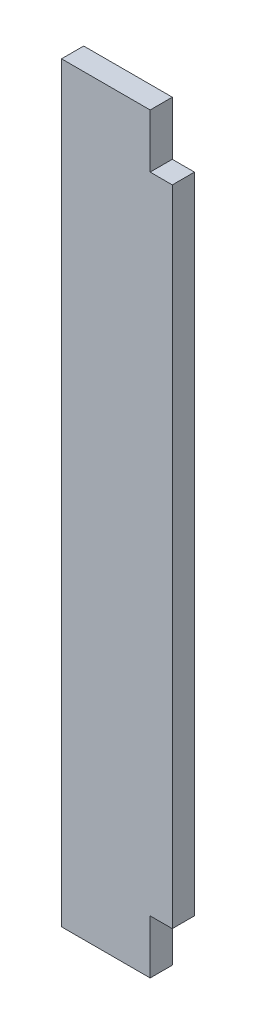
SolidWorks part; units mm, degrees
material "Pine"
ref_plane "Front Plane" through (0, 0, 0) normal (0, 0, 1) x (1, 0, 0)
ref_plane "Top Plane" through (0, 0, 0) normal (0, 1, 0) x (1, 0, 0)
ref_plane "Right Plane" through (0, 0, 0) normal (1, 0, 0) x (0, 0, -1)
sketch "Sketch1" plane through (0, 0, 0) normal (0, 0, 1) x (1, 0, 0)
  line L0 (8932.6508, -5243.5125) -> (10226.1458, -5243.5125)
  line L1 (9086.3208, -4722.0918) -> (10222.9708, -4853.7812)
  line L2 (8914.8708, -6342.0625) -> (10197.5708, -6342.0625)
  line L3 (8914.8708, -5808.6625) -> (10197.5708, -5808.6625)
  line L4 (8919.6333, -5253.0375) -> (10218.2083, -5253.0375)
  line L5 (9134.2633, -4656.1375) -> (9134.2633, -4638.3575)
  line L6 (9091.0833, -4638.3575) -> (9134.2633, -4638.3575)
  line L7 (9091.0833, -4567.2375) -> (9091.0833, -4638.3575)
  line L8 (9134.2633, -4656.1375) -> (9581.3033, -4656.1375)
  line L9 (9091.0833, -4567.2375) -> (9624.4833, -4567.2375)
  line L10 (9581.3033, -4656.1375) -> (9581.3033, -4638.3575)
  line L11 (9581.3033, -4638.3575) -> (9624.4833, -4638.3575)
  line L12 (9624.4833, -4567.2375) -> (9624.4833, -4638.3575)
  line L13 (8932.6508, -5225.7325) -> (9344.9775, -5225.7325)
  line L14 (8932.6508, -5256.2125) -> (8932.6508, -5243.5125)
  line L15 (8911.6958, -5256.2125) -> (8932.6508, -5256.2125)
  line L16 (8914.8708, -4722.0918) -> (9086.3208, -4722.0918)
  line L17 (8911.6958, -4715.5913) -> (8932.6508, -4715.5913)
  line L18 (8914.8708, -6342.0625) -> (8914.8708, -5808.6625)
  line L19 (12082.9917, -4722.0918) -> (10946.3417, -4853.7812)
  line L20 (12236.6617, -5243.5125) -> (10943.1667, -5243.5125)
  line L21 (10951.1042, -5253.0375) -> (12249.6792, -5253.0375)
  line L22 (10838.3917, -5656.2625) -> (11308.2917, -5656.2625)
  line L23 (10838.3917, -5719.7625) -> (11308.2917, -5719.7625)
  line L24 (10838.3917, -5742.5368) -> (11308.2917, -5742.5368)
  line L25 (10806.6417, -6342.0625) -> (11340.0417, -6342.0625)
  line L26 (10803.4667, -6335.7125) -> (11343.2167, -6335.7125)
  line L27 (10803.4667, -6317.9325) -> (11343.2167, -6317.9325)
  line L28 (10943.1667, -5225.7325) -> (11376.4483, -5225.7325)
  line L29 (11506.7292, -4754.5625) -> (10806.6417, -4827.5875)
  line L30 (11506.7292, -4567.2375) -> (11506.7292, -4754.5625)
  line L31 (10806.6417, -4567.2375) -> (10806.6417, -4827.5875)
  line L32 (10806.6417, -4567.2375) -> (11506.7292, -4567.2375)
  line L33 (10235.6708, -6329.3625) -> (10245.1958, -6329.3625)
  line L34 (10245.1958, -6329.3625) -> (10254.7208, -6278.5625)
  line L35 (10302.3458, -6329.3625) -> (10311.8708, -6278.5625)
  line L36 (10302.3458, -6329.3625) -> (10292.8208, -6329.3625)
  line L37 (10245.1958, -5821.3625) -> (10254.7208, -5872.1625)
  line L38 (10235.6708, -5821.3625) -> (10245.1958, -5821.3625)
  line L39 (10292.8208, -5821.3625) -> (10302.3458, -5821.3625)
  line L40 (10302.3458, -5821.3625) -> (10311.8708, -5872.1625)
  line L41 (10235.6708, -5821.3625) -> (10235.6708, -6329.3625)
  line L42 (10254.7208, -5872.1625) -> (10254.7208, -6278.5625)
  line L43 (10311.8708, -5872.1625) -> (10311.8708, -6278.5625)
  line L44 (10292.8208, -5821.3625) -> (10292.8208, -6329.3625)
  line L45 (8932.6508, -5225.7325) -> (8932.6508, -4715.5913)
  line L46 (8911.6958, -4715.5913) -> (8911.6958, -5256.2125)
  line L47 (8914.8708, -5248.275) -> (8914.8708, -4722.0918)
  line L48 (8919.6333, -5253.0375) -> (8914.8708, -5248.275)
  line L49 (8914.8708, -5145.0875) -> (8937.426, -5145.0875)
  line L50 (8914.8708, -5202.2375) -> (8937.426, -5202.2375)
  line L51 (10838.3917, -5656.2625) -> (10838.3917, -5719.7625)
  line L52 (10832.0417, -5736.1868) -> (10856.1717, -5736.1868)
  line L53 (10806.6417, -6342.0625) -> (10806.6417, -5818.7368)
  line L54 (10832.0417, -5649.9125) -> (10856.1717, -5649.9125)
  line L55 (10832.0417, -5726.1125) -> (10856.1717, -5726.1125)
  line L56 (10806.6417, -5818.7368) -> (10833.9015, -5818.7368)
  line L57 (10832.0417, -5806.0442) -> (10851.6815, -5806.0442)
  line L58 (10856.1717, -5801.5541) -> (10856.1717, -5736.1868)
  line L59 (10838.3917, -5814.2467) -> (10838.3917, -5742.5368)
  line L60 (10832.0417, -5806.0442) -> (10832.0417, -5736.1868)
  line L61 (10803.4667, -6317.9325) -> (10803.4667, -6335.7125)
  line L62 (10197.5708, -5808.6625) -> (10197.5708, -6342.0625)
  line L63 (9762.3842, -6348.4125) -> (9762.3842, -5802.3125)
  line L64 (9780.1642, -6348.4125) -> (9762.3842, -6348.4125)
  line L65 (9780.1642, -5802.3125) -> (9780.1642, -6348.4125)
  line L66 (9762.3842, -5802.3125) -> (9780.1642, -5802.3125)
  line L67 (9332.2775, -6348.4125) -> (9332.2775, -5802.3125)
  line L68 (9332.2775, -6348.4125) -> (9350.0575, -6348.4125)
  line L69 (9350.0575, -5802.3125) -> (9350.0575, -6348.4125)
  line L70 (9332.2775, -5802.3125) -> (9350.0575, -5802.3125)
  line L71 (9993.8374, -6061.075) -> (9993.8374, -6045.2418)
  line L72 (9998.5999, -6065.8375) -> (10014.4331, -6065.8375)
  line L73 (9998.5999, -6084.8875) -> (10014.4331, -6084.8875)
  line L74 (9993.8374, -6105.4832) -> (9993.8374, -6089.65)
  line L75 (9974.7874, -6105.4832) -> (9974.7874, -6089.65)
  line L76 (9954.1917, -6084.8875) -> (9970.0249, -6084.8875)
  line L77 (9974.7874, -6061.075) -> (9974.7874, -6045.2418)
  line L78 (9954.1917, -6065.8375) -> (9970.0249, -6065.8375)
  line L79 (10793.9417, -6237.2875) -> (10816.4969, -6237.2875)
  line L80 (10793.9417, -6294.4375) -> (10816.4969, -6294.4375)
  line L81 (10856.1717, -5649.9125) -> (10856.1717, -5726.1125)
  line L82 (10832.0417, -5726.1125) -> (10832.0417, -5649.9125)
  line L83 (10226.1458, -5225.7325) -> (10226.1458, -5243.5125)
  line L84 (10205.1908, -5257.8) -> (10205.1908, -4844.2499)
  line L85 (10230.9083, -4844.2499) -> (10230.9083, -5257.8)
  line L86 (10205.1908, -5257.8) -> (10230.9083, -5257.8)
  line L87 (10205.1908, -4844.2499) -> (10230.9083, -4844.2499)
  line L88 (10946.3417, -5176.8375) -> (10968.8969, -5176.8375)
  line L89 (9349.4676, -5141.9125) -> (9358.2674, -5141.9125)
  line L90 (10946.3417, -5119.6875) -> (10968.8969, -5119.6875)
  line L91 (9929.011, -4660.9635) -> (10066.0807, -4660.9635)
  line L92 (9929.011, -4678.7435) -> (10066.0807, -4678.7435)
  line L93 (10943.1667, -5225.7325) -> (10943.1667, -5243.5125)
  line L94 (10946.3417, -5248.275) -> (10951.1042, -5253.0375)
  line L95 (10946.3417, -5257.8063) -> (10946.3417, -4849.0188)
  line L96 (10964.1217, -5257.8) -> (10964.1217, -4844.2499)
  line L97 (10938.4042, -4844.2499) -> (10938.4042, -5257.8)
  line L98 (10938.4042, -5257.8) -> (10964.1217, -5257.8)
  line L99 (10964.1217, -4844.2499) -> (10938.4042, -4844.2499)
  line L100 (10344.8908, -4560.8875) -> (10369.0208, -4560.8875)
  line L101 (10344.8908, -4560.8875) -> (10369.0208, -4560.8875)
  line L102 (10800.2917, -4560.8875) -> (10824.4217, -4560.8875)
  line L103 (10200.4156, -5119.6875) -> (10222.9708, -5119.6875)
  line L104 (10200.4156, -5176.8375) -> (10222.9708, -5176.8375)
  line L105 (9344.9775, -5146.4026) -> (9344.9775, -5225.7325)
  line L106 (10344.8908, -4560.8875) -> (10344.8908, -4833.9375)
  line L107 (9792.8642, -5225.7325) -> (9792.8642, -5146.4026)
  line L108 (9362.7575, -5225.7325) -> (9775.0842, -5225.7325)
  line L109 (9680.3633, -4761.8396) -> (9680.3633, -4559.9604)
  line L110 (9656.2333, -4559.9604) -> (9680.3633, -4559.9604)
  line L111 (9656.2333, -4761.8396) -> (9680.3633, -4761.8396)
  line L112 (9656.2333, -4761.8396) -> (9656.2333, -4559.9604)
  line L113 (9779.5743, -5141.9125) -> (9788.374, -5141.9125)
  line L114 (10070.5708, -4665.4536) -> (10070.5708, -4674.2534)
  line L115 (9924.5208, -4674.2534) -> (9924.5208, -4665.4536)
  line L116 (12127.4417, -6188.3925) -> (12205.5015, -6188.3925)
  line L117 (12209.9917, -6170.6125) -> (12209.9917, -6183.9024)
  line L118 (9792.8642, -5225.7325) -> (10226.1458, -5225.7325)
  line L119 (9662.5833, -4754.5625) -> (10362.6708, -4827.5875)
  line L120 (9662.5833, -4567.2375) -> (9662.5833, -4754.5625)
  line L121 (10362.6708, -4567.2375) -> (10362.6708, -4827.5875)
  line L122 (9662.5833, -4567.2375) -> (10362.6708, -4567.2375)
  line L123 (10824.4217, -4833.9375) -> (10800.2917, -4833.9375)
  line L124 (10800.2917, -4833.9375) -> (10800.2917, -4560.8875)
  line L125 (10824.4217, -4560.8875) -> (10824.4217, -4833.9375)
  line L126 (10344.8908, -4833.9375) -> (10369.0208, -4833.9375)
  line L127 (10369.0208, -4833.9375) -> (10369.0208, -4560.8875)
  line L128 (10222.9708, -5248.275) -> (10218.2083, -5253.0375)
  line L129 (10222.9708, -5257.8063) -> (10222.9708, -4849.0188)
  line L130 (11734.6544, -5701.375) -> (11739.2301, -5701.375)
  line L131 (9362.7575, -5225.7325) -> (9362.7575, -5146.4026)
  line L132 (9775.0842, -5146.4026) -> (9775.0842, -5225.7325)
  line L133 (11761.3864, -5701.375) -> (11756.8282, -5701.375)
  line L134 (11734.6544, -5693.755) -> (11739.2301, -5693.755)
  line L135 (11761.4039, -5693.755) -> (11756.8282, -5693.755)
  line L136 (11734.6544, -5701.375) -> (11739.2301, -5701.375)
  line L137 (11744.3462, -5721.3024) -> (11744.3462, -5706.4179)
  line L138 (11751.7122, -5721.3024) -> (11751.7122, -5706.4179)
  line L139 (11740.0917, -6170.6125) -> (11740.0917, -6183.9024)
  line L140 (11689.2917, -6188.3925) -> (11822.6417, -6188.3925)
  line L141 (11689.2917, -6348.4093) -> (11689.2917, -6164.2657)
  line L142 (11689.2917, -6164.2657) -> (11746.4417, -6164.2657)
  line L143 (11746.4417, -6164.2657) -> (11746.4417, -6188.3925)
  line L144 (11689.2917, -6164.2657) -> (11746.4417, -6164.2657)
  line L145 (11340.0417, -5818.7368) -> (11340.0417, -6342.0625)
  line L146 (11290.5117, -5726.1125) -> (11314.6417, -5726.1125)
  line L147 (11290.5117, -5649.9125) -> (11290.5117, -5726.1125)
  line L148 (11340.0417, -5818.7368) -> (11312.7818, -5818.7368)
  line L149 (11314.6417, -5806.0442) -> (11295.0018, -5806.0442)
  line L150 (11290.5117, -5801.5541) -> (11290.5117, -5736.1868)
  line L151 (11308.2917, -5814.2467) -> (11308.2917, -5742.5368)
  line L152 (11314.6417, -5806.0442) -> (11314.6417, -5736.1868)
  line L153 (11290.5117, -5736.1868) -> (11314.6417, -5736.1868)
  line L154 (11848.0417, -6267.1325) -> (11962.3417, -6267.1325)
  line L155 (11962.3417, -6267.1325) -> (11962.3417, -6203.6325)
  line L156 (11343.2167, -6317.9325) -> (11343.2167, -6335.7125)
  line L157 (11365.4417, -5656.2625) -> (11365.4417, -5719.7625)
  line L158 (11365.4417, -5656.2625) -> (11479.7417, -5656.2625)
  line L159 (11778.1917, -6071.3937) -> (11802.3217, -6071.3937)
  line L160 (11314.6417, -5726.1125) -> (11314.6417, -5649.9125)
  line L161 (11314.6417, -5649.9125) -> (11290.5117, -5649.9125)
  line L162 (11308.2917, -5719.7625) -> (11308.2917, -5656.2625)
  line L163 (11689.2917, -6348.4093) -> (11713.4217, -6348.4093)
  line L164 (12203.6417, -6164.2657) -> (12260.7917, -6164.2657)
  line L165 (11713.4217, -6348.4093) -> (11713.4217, -6164.2657)
  line L166 (11695.6417, -6342.0625) -> (11695.6417, -6170.6125)
  line L167 (11695.6417, -6048.5337) -> (11699.4517, -6052.3437)
  line L168 (11822.6417, -6292.5325) -> (11822.6417, -6188.3925)
  line L169 (11695.6417, -6342.0625) -> (11695.6417, -6170.6125)
  line L170 (11848.0417, -6203.6325) -> (11962.3417, -6203.6325)
  line L171 (11848.0417, -6203.6325) -> (11848.0417, -6267.1325)
  line L172 (11987.7417, -6267.1325) -> (11987.7417, -6203.6325)
  line L173 (11784.5417, -6077.7437) -> (11784.5417, -6141.2438)
  line L174 (11517.8417, -5656.2625) -> (11632.1417, -5656.2625)
  line L175 (11632.1417, -5656.2625) -> (11632.1417, -5719.7625)
  line L176 (11632.1417, -5719.7625) -> (11517.8417, -5719.7625)
  line L177 (11517.8417, -5719.7625) -> (11517.8417, -5656.2625)
  line L178 (11692.4667, -6028.2137) -> (11692.4667, -6045.9937)
  line L179 (11695.6417, -5979.3188) -> (11718.1969, -5979.3188)
  line L180 (11695.6417, -5922.1687) -> (11718.1969, -5922.1687)
  line L181 (11821.0415, -5722.9375) -> (11821.0415, -5943.6)
  line L182 (11687.7042, -5651.5) -> (11701.9917, -5651.5)
  line L183 (11687.7042, -5651.5) -> (11687.7042, -6055.5251)
  line L184 (11687.7042, -6055.5251) -> (11701.9917, -6055.5251)
  line L185 (11701.9917, -6055.5251) -> (11701.9917, -5651.5)
  line L186 (11695.6417, -6055.2013) -> (11695.6417, -5649.595)
  line L187 (11695.6417, -5656.2625) -> (11695.6417, -6048.5337)
  line L188 (11695.6417, -6170.6125) -> (11740.0917, -6170.6125)
  line L189 (12203.6417, -6164.2657) -> (12203.6417, -6188.3925)
  line L190 (12254.4417, -6342.0625) -> (12254.4417, -6170.6125)
  line L191 (12129.0419, -5943.6) -> (12129.0419, -5722.9375)
  line L192 (12254.4417, -6048.5337) -> (12250.6317, -6052.3437)
  line L193 (12257.6167, -6045.9937) -> (12257.6167, -6028.2137)
  line L194 (12248.0917, -5651.5) -> (12262.3792, -5651.5)
  line L195 (12262.3792, -5651.5) -> (12262.3792, -6055.5251)
  line L196 (12262.3792, -6055.5251) -> (12248.0917, -6055.5251)
  line L197 (12248.0917, -6055.5251) -> (12248.0917, -5651.5)
  line L198 (12254.4417, -6141.2438) -> (12254.4417, -6077.7437)
  line L199 (12236.6617, -6164.2657) -> (12260.7917, -6164.2657)
  line L200 (12102.0417, -6267.1325) -> (11987.7417, -6267.1325)
  line L201 (11330.1865, -6237.2875) -> (11352.7417, -6237.2875)
  line L202 (11330.1865, -6294.4375) -> (11352.7417, -6294.4375)
  line L203 (11474.6617, -5851.8425) -> (11492.4417, -5851.8425)
  line L204 (11474.6617, -5808.6625) -> (11474.6617, -5851.8425)
  line L205 (11403.5417, -5808.6625) -> (11474.6617, -5808.6625)
  line L206 (11492.4417, -5851.8425) -> (11492.4417, -6298.8825)
  line L207 (11403.5417, -6342.0625) -> (11403.5417, -5808.6625)
  line L208 (11474.6617, -6298.8825) -> (11492.4417, -6298.8825)
  line L209 (11474.6617, -6342.0625) -> (11474.6617, -6298.8825)
  line L210 (11403.5417, -6342.0625) -> (11474.6617, -6342.0625)
  line L211 (11619.4417, -5851.8425) -> (11601.6617, -5851.8425)
  line L212 (11601.6617, -5808.6625) -> (11601.6617, -5851.8425)
  line L213 (11530.5417, -5808.6625) -> (11601.6617, -5808.6625)
  line L214 (11619.4417, -5851.8425) -> (11619.4417, -6298.8825)
  line L215 (11530.5417, -6342.0625) -> (11530.5417, -5808.6625)
  line L216 (11619.4417, -6298.8825) -> (11601.6617, -6298.8825)
  line L217 (11601.6617, -6342.0625) -> (11601.6617, -6298.8825)
  line L218 (11530.5417, -6342.0625) -> (11601.6617, -6342.0625)
  line L219 (11479.7417, -5719.7625) -> (11479.7417, -5656.2625)
  line L220 (11365.4417, -5719.7625) -> (11479.7417, -5719.7625)
  line L221 (11778.1917, -6147.5937) -> (11802.3217, -6147.5937)
  line L222 (11802.3217, -6071.3937) -> (11802.3217, -6147.5937)
  line L223 (11778.1917, -6147.5937) -> (11778.1917, -6071.3937)
  line L224 (12254.4417, -5922.1687) -> (12231.8865, -5922.1687)
  line L225 (12254.4417, -5979.3188) -> (12231.8865, -5979.3188)
  line L226 (12254.4417, -6055.2013) -> (12254.4417, -5649.595)
  line L227 (12254.4417, -6048.5337) -> (12254.4417, -5656.2625)
  line L228 (11841.6917, -5702.2873) -> (12108.3917, -5702.2873)
  line L229 (11822.6417, -6292.5325) -> (12127.4417, -6292.5325)
  line L230 (12127.4417, -6292.5325) -> (12127.4417, -6188.3925)
  line L231 (12254.4417, -6170.6125) -> (12209.9917, -6170.6125)
  line L232 (11695.6417, -6342.0625) -> (12254.4417, -6342.0625)
  line L233 (12236.6617, -6348.4093) -> (12260.7917, -6348.4093)
  line L234 (12260.7917, -6348.4093) -> (12260.7917, -6164.2657)
  line L235 (12236.6617, -6348.4093) -> (12236.6617, -6164.2657)
  line L236 (12102.0417, -6203.6325) -> (12102.0417, -6267.1325)
  line L237 (11987.7417, -6203.6325) -> (12102.0417, -6203.6325)
  line L238 (12236.6617, -6147.5937) -> (12236.6617, -6071.3937)
  line L239 (12203.6417, -6188.3925) -> (12260.7917, -6188.3925)
  line L240 (11098.7417, -4665.4536) -> (11098.7417, -4674.2534)
  line L241 (11394.2283, -5146.4026) -> (11394.2283, -5225.7325)
  line L242 (11376.4483, -5225.7325) -> (11376.4483, -5146.4026)
  line L243 (11394.2283, -5225.7325) -> (11806.555, -5225.7325)
  line L244 (11841.6917, -5964.2502) -> (12108.3917, -5964.2502)
  line L245 (12236.6617, -6147.5937) -> (12260.7917, -6147.5937)
  line L246 (12236.6617, -5256.2125) -> (12236.6617, -5243.5125)
  line L247 (12260.7917, -6147.5937) -> (12260.7917, -6071.3937)
  line L248 (12260.7917, -6071.3937) -> (12236.6617, -6071.3937)
  line L249 (12254.4417, -6077.7437) -> (11784.5417, -6077.7437)
  line L250 (11784.5417, -6141.2438) -> (12254.4417, -6141.2438)
  line L252 (12254.4417, -5656.2625) -> (11695.6417, -5656.2625)
  line L253 (11699.4517, -6052.3437) -> (12250.6317, -6052.3437)
  line L254 (11692.4667, -6045.9937) -> (12257.6167, -6045.9937)
  line L255 (11692.4667, -6028.2137) -> (12257.6167, -6028.2137)
  line L256 (11824.335, -5146.4026) -> (11824.335, -5225.7325)
  line L257 (11811.0451, -5141.9125) -> (11819.8449, -5141.9125)
  line L258 (11244.7917, -4674.2534) -> (11244.7917, -4665.4536)
  line L259 (11806.555, -5225.7325) -> (11806.555, -5146.4026)
  line L260 (11488.9492, -4761.8396) -> (11488.9492, -4559.9604)
  line L261 (11488.9492, -4559.9604) -> (11513.0792, -4559.9604)
  line L262 (11488.9492, -4761.8396) -> (11513.0792, -4761.8396)
  line L263 (11513.0792, -4761.8396) -> (11513.0792, -4559.9604)
  line L264 (11240.3015, -4660.9635) -> (11103.2318, -4660.9635)
  line L265 (11103.2318, -4678.7435) -> (11240.3015, -4678.7435)
  line L266 (12236.6617, -5225.7325) -> (12236.6617, -4715.5913)
  line L267 (12257.6167, -4715.5913) -> (12257.6167, -5256.2125)
  line L268 (12254.4417, -5248.275) -> (12254.4417, -4722.0918)
  line L269 (12236.6617, -5225.7325) -> (11824.335, -5225.7325)
  line L270 (12035.0492, -4656.1375) -> (12035.0492, -4638.3575)
  line L271 (12078.2292, -4638.3575) -> (12035.0492, -4638.3575)
  line L272 (12078.2292, -4567.2375) -> (12078.2292, -4638.3575)
  line L273 (12035.0492, -4656.1375) -> (11588.0092, -4656.1375)
  line L274 (11544.8292, -4567.2375) -> (12078.2292, -4567.2375)
  line L275 (11588.0092, -4656.1375) -> (11588.0092, -4638.3575)
  line L276 (11544.8292, -4638.3575) -> (11588.0092, -4638.3575)
  line L277 (11544.8292, -4567.2375) -> (11544.8292, -4638.3575)
  line L278 (12249.6792, -5253.0375) -> (12254.4417, -5248.275)
  line L280 (12257.6167, -5256.2125) -> (12236.6617, -5256.2125)
  line L281 (12231.8865, -5145.0875) -> (12254.4417, -5145.0875)
  line L282 (12231.8865, -5202.2375) -> (12254.4417, -5202.2375)
  line L283 (12236.6617, -4715.5913) -> (12257.6167, -4715.5913)
  line L284 (12082.9917, -4722.0918) -> (12254.4417, -4722.0918)
  line L285 (11380.9385, -5141.9125) -> (11389.7382, -5141.9125)
  circle A0 centre (8923.7608, -4778.9042) radius 1.5875
  circle A1 centre (9062.6598, -4736.3765) radius 2.3685
  circle A2 centre (9051.3958, -6281.7375) radius 22.225
  circle A3 centre (9083.1458, -6249.9875) radius 1.5875
  circle A4 centre (9083.1458, -6313.4875) radius 1.5875
  circle A5 centre (9019.6458, -6249.9875) radius 1.5875
  circle A6 centre (9019.6458, -6313.4875) radius 1.5875
  circle A7 centre (8972.3383, -5202.2375) radius 1.5875
  circle A8 centre (8923.7608, -5015.9708) radius 1.5875
  circle A9 centre (8923.7608, -5134.5042) radius 1.5875
  circle A10 centre (9054.5708, -5234.6225) radius 1.5875
  circle A11 centre (8923.7608, -4897.4375) radius 1.5875
  circle A12 centre (8972.3383, -5087.9375) radius 1.5875
  circle A13 centre (8972.3383, -5145.0875) radius 1.5875
  circle A14 centre (10847.2817, -5668.9625) radius 1.5875
  circle A15 centre (10847.2817, -5707.0625) radius 1.5875
  circle A16 centre (10847.2817, -5755.2368) radius 1.5875
  circle A17 centre (10851.4092, -6237.2875) radius 1.5875
  circle A18 centre (10851.4092, -6294.4375) radius 1.5875
  circle A19 centre (10847.2817, -5793.3442) radius 1.5875
  arc A20 (10833.9015, -5818.7368) -> (10838.3917, -5814.2467) centre (10836.1466, -5816.4918) ccw
  arc A21 (10851.6815, -5806.0442) -> (10856.1717, -5801.5541) centre (10853.9266, -5803.7992) ccw
  circle A22 centre (10882.8417, -6040.4375) radius 1.5875
  circle A23 centre (10882.8417, -6218.2375) radius 1.5875
  circle A24 centre (10882.8417, -5862.6375) radius 1.5875
  circle A25 centre (10908.2417, -6326.8225) radius 1.5875
  circle A26 centre (10908.2417, -6326.8225) radius 1.5875
  circle A27 centre (10851.4092, -6180.1375) radius 1.5875
  circle A28 centre (10815.5317, -4783.4231) radius 1.5875
  circle A29 centre (10815.5317, -4696.9488) radius 1.5875
  circle A30 centre (10815.5317, -4610.4746) radius 1.5875
  circle A31 centre (10979.1323, -4867.0082) radius 2.3685
  circle A32 centre (10190.1802, -4867.0082) radius 2.3685
  circle A33 centre (10955.2317, -4929.9812) radius 1.5875
  circle A34 centre (10955.2317, -5031.5812) radius 1.5875
  circle A35 centre (10214.0808, -4929.9812) radius 1.5875
  circle A36 centre (10214.0808, -5031.5812) radius 1.5875
  circle A37 centre (9341.1675, -6265.8625) radius 1.5875
  circle A38 centre (9771.2742, -5884.8625) radius 1.5875
  circle A39 centre (9771.2742, -6138.8625) radius 1.5875
  circle A40 centre (9771.2742, -6011.8625) radius 1.5875
  arc A41 (10036.2287, -6113.8083) -> (10051.3426, -6111.6033) centre (10042.9639, -6107.0732) ccw
  arc A42 (10051.3426, -6111.6033) -> (10051.3426, -6039.1217) centre (9984.3124, -6075.3625) ccw
  arc A43 (10051.3426, -6039.1217) -> (10036.2287, -6036.9167) centre (10042.9639, -6043.6518) ccw
  arc A44 (10034.5851, -6102.5431) -> (10034.5851, -6048.1819) centre (9984.3124, -6075.3625) ccw
  arc A45 (10034.5851, -6102.5431) -> (10036.2287, -6113.8083) centre (10042.9639, -6107.0732) ccw
  arc A46 (10036.2287, -6036.9167) -> (10034.5851, -6048.1819) centre (10042.9639, -6043.6518) ccw
  arc A47 (9945.8666, -6127.2787) -> (9948.0717, -6142.3927) centre (9952.6018, -6134.0139) ccw
  arc A48 (9948.0717, -6142.3927) -> (10020.5532, -6142.3927) centre (9984.3124, -6075.3625) ccw
  arc A49 (10020.5532, -6142.3927) -> (10022.7583, -6127.2787) centre (10016.0231, -6134.0139) ccw
  arc A50 (9957.1319, -6125.6352) -> (10011.493, -6125.6352) centre (9984.3124, -6075.3625) ccw
  arc A51 (9957.1319, -6125.6352) -> (9945.8666, -6127.2787) centre (9952.6018, -6134.0139) ccw
  arc A52 (10022.7583, -6127.2787) -> (10011.493, -6125.6352) centre (10016.0231, -6134.0139) ccw
  arc A53 (9932.3962, -6036.9167) -> (9917.2822, -6039.1217) centre (9925.661, -6043.6518) ccw
  arc A54 (9917.2822, -6039.1217) -> (9917.2822, -6111.6033) centre (9984.3124, -6075.3625) ccw
  arc A55 (9917.2822, -6111.6033) -> (9932.3962, -6113.8083) centre (9925.661, -6107.0732) ccw
  arc A56 (9934.0398, -6048.1819) -> (9934.0398, -6102.5431) centre (9984.3124, -6075.3625) ccw
  arc A57 (9934.0398, -6048.1819) -> (9932.3962, -6036.9167) centre (9925.661, -6043.6518) ccw
  arc A58 (9932.3962, -6113.8083) -> (9934.0398, -6102.5431) centre (9925.661, -6107.0732) ccw
  arc A59 (9945.8666, -6023.4463) -> (9957.1319, -6025.0898) centre (9952.6018, -6016.7111) ccw
  arc A60 (10011.493, -6025.0898) -> (10022.7583, -6023.4463) centre (10016.0231, -6016.7111) ccw
  arc A61 (10011.493, -6025.0898) -> (9957.1319, -6025.0898) centre (9984.3124, -6075.3625) ccw
  arc A62 (9948.0717, -6008.3323) -> (9945.8666, -6023.4463) centre (9952.6018, -6016.7111) ccw
  arc A63 (10020.5532, -6008.3323) -> (9948.0717, -6008.3323) centre (9984.3124, -6075.3625) ccw
  arc A64 (10022.7583, -6023.4463) -> (10020.5532, -6008.3323) centre (10016.0231, -6016.7111) ccw
  arc A65 (10005.0943, -6187.7574) -> (10096.7073, -6096.1443) centre (9984.3124, -6075.3625) ccw
  arc A66 (9993.8374, -6178.3911) -> (10005.0943, -6187.7574) centre (10003.3624, -6178.3911) ccw
  arc A67 (10001.6306, -6169.0249) -> (10077.9748, -6092.6807) centre (9984.3124, -6075.3625) ccw
  arc A68 (10087.3411, -6084.8875) -> (10077.9748, -6092.6807) centre (10087.3411, -6094.4125) ccw
  arc A69 (10001.6306, -6169.0249) -> (9993.8374, -6178.3911) centre (10003.3624, -6178.3911) ccw
  arc A70 (9963.5306, -6187.7574) -> (9974.7874, -6178.3911) centre (9965.2624, -6178.3911) ccw
  arc A71 (9871.9176, -6096.1443) -> (9963.5306, -6187.7574) centre (9984.3124, -6075.3625) ccw
  arc A72 (9881.2838, -6084.8875) -> (9871.9176, -6096.1443) centre (9881.2838, -6094.4125) ccw
  arc A73 (9890.65, -6092.6807) -> (9966.9943, -6169.0249) centre (9984.3124, -6075.3625) ccw
  arc A74 (9974.7874, -6178.3911) -> (9966.9943, -6169.0249) centre (9965.2624, -6178.3911) ccw
  arc A75 (9890.65, -6092.6807) -> (9881.2838, -6084.8875) centre (9881.2838, -6094.4125) ccw
  arc A76 (9871.9176, -6054.5807) -> (9881.2838, -6065.8375) centre (9881.2838, -6056.3125) ccw
  arc A77 (9963.5306, -5962.9676) -> (9871.9176, -6054.5807) centre (9984.3124, -6075.3625) ccw
  arc A78 (9974.7874, -5972.3339) -> (9963.5306, -5962.9676) centre (9965.2624, -5972.3339) ccw
  arc A79 (9966.9943, -5981.7001) -> (9890.65, -6058.0443) centre (9984.3124, -6075.3625) ccw
  arc A80 (9881.2838, -6065.8375) -> (9890.65, -6058.0443) centre (9881.2838, -6056.3125) ccw
  arc A81 (9966.9943, -5981.7001) -> (9974.7874, -5972.3339) centre (9965.2624, -5972.3339) ccw
  arc A82 (10077.9748, -6058.0443) -> (10087.3411, -6065.8375) centre (10087.3411, -6056.3125) ccw
  arc A83 (9993.8374, -5972.3339) -> (10001.6306, -5981.7001) centre (10003.3624, -5972.3339) ccw
  arc A84 (10077.9748, -6058.0443) -> (10001.6306, -5981.7001) centre (9984.3124, -6075.3625) ccw
  arc A85 (10087.3411, -6065.8375) -> (10096.7073, -6054.5807) centre (10087.3411, -6056.3125) ccw
  arc A86 (10096.7073, -6054.5807) -> (10005.0943, -5962.9676) centre (9984.3124, -6075.3625) ccw
  arc A87 (10005.0943, -5962.9676) -> (9993.8374, -5972.3339) centre (10003.3624, -5972.3339) ccw
  arc A88 (10014.4331, -6065.8375) -> (10018.7361, -6059.0339) centre (10014.4331, -6061.075) ccw
  arc A89 (10018.7361, -6059.0339) -> (10000.641, -6040.9388) centre (9984.3124, -6075.3625) ccw
  arc A90 (10000.641, -6040.9388) -> (9993.8374, -6045.2418) centre (9998.5999, -6045.2418) ccw
  arc A91 (9993.8374, -6061.075) -> (9998.5999, -6065.8375) centre (9998.5999, -6061.075) ccw
  arc A92 (9993.8374, -6105.4832) -> (10000.641, -6109.7862) centre (9998.5999, -6105.4832) ccw
  arc A93 (10000.641, -6109.7862) -> (10018.7361, -6091.6911) centre (9984.3124, -6075.3625) ccw
  arc A94 (10018.7361, -6091.6911) -> (10014.4331, -6084.8875) centre (10014.4331, -6089.65) ccw
  arc A95 (9998.5999, -6084.8875) -> (9993.8374, -6089.65) centre (9998.5999, -6089.65) ccw
  arc A96 (9954.1917, -6084.8875) -> (9949.8888, -6091.6911) centre (9954.1917, -6089.65) ccw
  arc A97 (9949.8888, -6091.6911) -> (9967.9839, -6109.7862) centre (9984.3124, -6075.3625) ccw
  arc A98 (9967.9839, -6109.7862) -> (9974.7874, -6105.4832) centre (9970.0249, -6105.4832) ccw
  arc A99 (9974.7874, -6089.65) -> (9970.0249, -6084.8875) centre (9970.0249, -6089.65) ccw
  arc A100 (9970.0249, -6065.8375) -> (9974.7874, -6061.075) centre (9970.0249, -6061.075) ccw
  arc A101 (9949.8888, -6059.0339) -> (9954.1917, -6065.8375) centre (9954.1917, -6061.075) ccw
  arc A102 (9967.9839, -6040.9388) -> (9949.8888, -6059.0339) centre (9984.3124, -6075.3625) ccw
  arc A103 (9974.7874, -6045.2418) -> (9967.9839, -6040.9388) centre (9970.0249, -6045.2418) ccw
  arc A104 (10096.7073, -6096.1443) -> (10087.3411, -6084.8875) centre (10087.3411, -6094.4125) ccw
  circle A105 centre (9771.2742, -6265.8625) radius 1.5875
  circle A106 centre (9341.1675, -5884.8625) radius 1.5875
  circle A107 centre (9341.1675, -6138.8625) radius 1.5875
  circle A108 centre (9341.1675, -6011.8625) radius 1.5875
  circle A109 centre (11037.2315, -4887.5494) radius 15.0812
  arc A110 (9349.4676, -5141.9125) -> (9344.9775, -5146.4026) centre (9347.2226, -5144.1576) ccw
  arc A111 (9362.7575, -5146.4026) -> (9358.2674, -5141.9125) centre (9360.5124, -5144.1576) ccw
  circle A112 centre (9946.7458, -4669.8535) radius 1.5875
  arc A113 (9924.5208, -4674.2534) -> (9929.011, -4678.7435) centre (9926.7659, -4676.4984) ccw
  circle A114 centre (11003.8092, -5176.8375) radius 1.5875
  circle A115 centre (11003.8092, -5119.6875) radius 1.5875
  circle A116 centre (10353.7808, -4696.9488) radius 1.5875
  circle A117 centre (10353.7808, -4610.4746) radius 1.5875
  circle A118 centre (10353.7808, -4783.4231) radius 1.5875
  circle A119 centre (11003.8092, -5062.5375) radius 1.5875
  circle A120 centre (9353.8675, -5160.9625) radius 1.5875
  circle A121 centre (9638.7708, -5234.6225) radius 1.5875
  circle A122 centre (9671.4733, -4724.1144) radius 1.5875
  circle A123 centre (9671.4733, -4661.3637) radius 1.5875
  circle A124 centre (9671.4733, -4598.6129) radius 1.5875
  arc A125 (9792.8642, -5146.4026) -> (9788.374, -5141.9125) centre (9790.6191, -5144.1576) ccw
  arc A126 (9779.5743, -5141.9125) -> (9775.0842, -5146.4026) centre (9777.3292, -5144.1576) ccw
  circle A127 centre (10048.3458, -4669.8535) radius 1.5875
  arc A128 (10070.5708, -4665.4536) -> (10066.0807, -4660.9635) centre (10068.3258, -4663.2086) ccw
  arc A129 (10066.0807, -4678.7435) -> (10070.5708, -4674.2534) centre (10068.3258, -4676.4984) ccw
  circle A130 centre (9997.5458, -4669.8535) radius 1.5875
  arc A131 (9929.011, -4660.9635) -> (9924.5208, -4665.4536) centre (9926.7659, -4663.2086) ccw
  circle A132 centre (10132.081, -4887.5494) radius 15.0812
  circle A133 centre (10165.5033, -5176.8375) radius 1.5875
  circle A134 centre (10165.5033, -5119.6875) radius 1.5875
  circle A135 centre (9486.3708, -5234.6225) radius 1.5875
  circle A136 centre (10165.5033, -5062.5375) radius 1.5875
  circle A137 centre (9206.9708, -5234.6225) radius 1.5875
  circle A138 centre (10070.5708, -5234.6225) radius 1.5875
  circle A139 centre (9918.1708, -5234.6225) radius 1.5875
  circle A140 centre (9783.9742, -5160.9625) radius 1.5875
  circle A141 centre (9783.9742, -5193.9825) radius 1.5875
  circle A142 centre (9353.8675, -5193.9825) radius 1.5875
  circle A143 centre (11073.3417, -6326.8225) radius 1.5875
  circle A144 centre (11073.3417, -6326.8225) radius 1.5875
  circle A145 centre (11295.2742, -6180.1375) radius 1.5875
  circle A146 centre (11295.2742, -6294.4375) radius 1.5875
  circle A147 centre (11295.2742, -6237.2875) radius 1.5875
  circle A148 centre (11975.0417, -5692.775) radius 3.4925
  circle A149 centre (11263.8417, -5862.6375) radius 1.5875
  arc A150 (11739.2301, -5701.375) -> (11744.3462, -5706.4179) centre (11748.0292, -5697.565) ccw
  arc A151 (11751.7122, -5706.4179) -> (11756.8282, -5701.375) centre (11748.0292, -5697.565) ccw
  arc A152 (11744.3462, -5721.3024) -> (11751.7122, -5721.3024) centre (11748.0292, -5725.505) ccw
  arc A153 (11734.6544, -5693.755) -> (11724.9787, -5697.565) centre (11730.5667, -5697.565) ccw
  arc A154 (11756.8282, -5693.755) -> (11739.2301, -5693.755) centre (11748.0292, -5697.565) ccw
  arc A155 (11724.9787, -5697.565) -> (11734.6544, -5701.375) centre (11730.5667, -5697.565) ccw
  arc A156 (11761.3864, -5701.375) -> (11771.0797, -5697.565) centre (11765.4842, -5697.565) ccw
  arc A157 (11771.0797, -5697.565) -> (11761.4039, -5693.755) centre (11765.4917, -5697.565) ccw
  arc A158 (11740.0917, -6183.9024) -> (11744.5818, -6188.3925) centre (11742.3367, -6186.1474) ccw
  arc A159 (12205.5015, -6188.3925) -> (12209.9917, -6183.9024) centre (12207.7466, -6186.1474) ccw
  circle A160 centre (11299.4017, -5793.3442) radius 1.5875
  arc A161 (11308.2917, -5814.2467) -> (11312.7818, -5818.7368) centre (11310.5367, -5816.4918) ccw
  arc A162 (11290.5117, -5801.5541) -> (11295.0018, -5806.0442) centre (11292.7567, -5803.7992) ccw
  circle A163 centre (11704.5317, -6314.149) radius 1.5875
  circle A164 centre (11748.9817, -6208.7125) radius 1.5875
  circle A165 centre (11263.8417, -6218.2375) radius 1.5875
  circle A166 centre (11263.8417, -6040.4375) radius 1.5875
  circle A167 centre (11238.4417, -6326.8225) radius 1.5875
  circle A168 centre (11238.4417, -6326.8225) radius 1.5875
  circle A169 centre (11299.4017, -5668.9625) radius 1.5875
  circle A170 centre (11299.4017, -5707.0625) radius 1.5875
  circle A171 centre (11726.7567, -6179.5025) radius 1.5875
  circle A172 centre (11704.5317, -6199.3198) radius 1.5875
  circle A173 centre (11748.9817, -6272.2125) radius 1.5875
  circle A174 centre (11704.5317, -6256.7344) radius 1.5875
  circle A175 centre (11299.4017, -5755.2368) radius 1.5875
  circle A176 centre (11913.4467, -6301.4225) radius 1.5875
  circle A177 centre (11790.2567, -6301.4225) radius 1.5875
  circle A178 centre (11793.4317, -6128.5437) radius 1.5875
  circle A179 centre (11753.1092, -5865.0188) radius 1.5875
  circle A180 centre (11809.9417, -6037.1038) radius 1.5875
  circle A181 centre (11809.9417, -6037.1038) radius 1.5875
  circle A182 centre (11753.1092, -5922.1687) radius 1.5875
  circle A183 centre (11975.0417, -5973.7625) radius 3.4925
  circle A184 centre (11975.0417, -6037.1038) radius 1.5875
  circle A185 centre (11753.1092, -5979.3188) radius 1.5875
  circle A186 centre (11975.0417, -6037.1038) radius 1.5875
  arc A187 (11841.6917, -5702.2873) -> (11821.0415, -5722.9375) centre (11841.6917, -5722.9375) ccw
  circle A188 centre (11811.5292, -5833.2687) radius 3.4925
  arc A189 (11821.0415, -5943.6) -> (11841.6917, -5964.2502) centre (11841.6917, -5943.6) ccw
  circle A190 centre (12196.9742, -5865.0188) radius 1.5875
  arc A191 (12129.0419, -5722.9375) -> (12108.3917, -5702.2873) centre (12108.3917, -5722.9375) ccw
  circle A192 centre (12036.6367, -6301.4225) radius 1.5875
  circle A193 centre (12159.8267, -6301.4225) radius 1.5875
  circle A194 centre (12138.5542, -5833.2687) radius 3.4925
  circle A195 centre (12197.2917, -5761.0375) radius 15.0812
  circle A196 centre (11793.4317, -6090.4437) radius 1.5875
  circle A197 centre (12196.9742, -5922.1687) radius 1.5875
  arc A198 (12108.3917, -5964.2502) -> (12129.0419, -5943.6) centre (12108.3917, -5943.6) ccw
  circle A199 centre (12196.9742, -5979.3188) radius 1.5875
  circle A200 centre (12201.1017, -6272.2125) radius 1.5875
  circle A201 centre (12245.5517, -6314.149) radius 1.5875
  circle A202 centre (12245.5517, -6256.7344) radius 1.5875
  circle A203 centre (12201.1017, -6208.7125) radius 1.5875
  circle A204 centre (12223.3267, -6179.5025) radius 1.5875
  circle A205 centre (12245.5517, -6199.3198) radius 1.5875
  circle A206 centre (11171.7667, -4669.8535) radius 1.5875
  circle A207 centre (11222.5667, -4669.8535) radius 1.5875
  arc A208 (11240.3015, -4678.7435) -> (11244.7917, -4674.2534) centre (11242.5466, -4676.4984) ccw
  circle A209 centre (11385.3383, -5193.9825) radius 1.5875
  circle A210 centre (12106.6527, -4736.3765) radius 2.3685
  circle A211 centre (12140.1417, -6037.1038) radius 1.5875
  circle A212 centre (12140.1417, -6037.1038) radius 1.5875
  circle A213 centre (12245.5517, -6090.4437) radius 1.5875
  circle A214 centre (12245.5517, -6128.5437) radius 1.5875
  circle A215 centre (11385.3383, -5160.9625) radius 1.5875
  arc A216 (11824.335, -5146.4026) -> (11819.8449, -5141.9125) centre (11822.0899, -5144.1576) ccw
  arc A217 (11811.0451, -5141.9125) -> (11806.555, -5146.4026) centre (11808.8001, -5144.1576) ccw
  circle A218 centre (11815.445, -5193.9825) radius 1.5875
  circle A219 centre (11815.445, -5160.9625) radius 1.5875
  circle A220 centre (11530.5417, -5234.6225) radius 1.5875
  circle A221 centre (11962.3417, -5234.6225) radius 1.5875
  arc A222 (11244.7917, -4665.4536) -> (11240.3015, -4660.9635) centre (11242.5466, -4663.2086) ccw
  circle A223 centre (11682.9417, -5234.6225) radius 1.5875
  circle A224 centre (11497.8392, -4724.1144) radius 1.5875
  circle A225 centre (11497.8392, -4661.3637) radius 1.5875
  circle A226 centre (11497.8392, -4598.6129) radius 1.5875
  circle A227 centre (11120.9667, -4669.8535) radius 1.5875
  arc A228 (11103.2318, -4660.9635) -> (11098.7417, -4665.4536) centre (11100.9867, -4663.2086) ccw
  arc A229 (11098.7417, -4674.2534) -> (11103.2318, -4678.7435) centre (11100.9867, -4676.4984) ccw
  circle A230 centre (12196.9742, -5202.2375) radius 1.5875
  circle A231 centre (12245.5517, -5015.9708) radius 1.5875
  circle A232 centre (12245.5517, -5134.5042) radius 1.5875
  circle A233 centre (12114.7417, -5234.6225) radius 1.5875
  circle A234 centre (12245.5517, -4897.4375) radius 1.5875
  circle A235 centre (12245.5517, -4778.9042) radius 1.5875
  circle A236 centre (12196.9742, -5087.9375) radius 1.5875
  circle A237 centre (12196.9742, -5145.0875) radius 1.5875
  circle A238 centre (11098.7417, -5234.6225) radius 1.5875
  circle A239 centre (11251.1417, -5234.6225) radius 1.5875
  arc A240 (11380.9385, -5141.9125) -> (11376.4483, -5146.4026) centre (11378.6934, -5144.1576) ccw
  arc A241 (11394.2283, -5146.4026) -> (11389.7382, -5141.9125) centre (11391.9833, -5144.1576) ccw
sketch "Sketch2" plane through (0, 0, 0) normal (0, 0, 1) x (1, 0, 0)
  line L0 (11403.5417, -6411.9125) -> (11474.6617, -6411.9125)
  line L1 (11474.6617, -6411.9125) -> (11474.6617, -6368.7325)
  line L2 (11474.6617, -6368.7325) -> (11492.4417, -6368.7325)
  line L3 (11492.4417, -6368.7325) -> (11492.4417, -5851.8425)
  line L4 (11492.4417, -5851.8425) -> (11474.6617, -5851.8425)
  line L5 (11474.6617, -5851.8425) -> (11474.6617, -5808.6625)
  line L6 (11474.6617, -5808.6625) -> (11403.5417, -5808.6625)
  line L7 (11403.5417, -5808.6625) -> (11403.5417, -6411.9125)
  dimension "D1" = 603.25
  dimension "D2" = 43.18
  dimension "D3" = 88.9
  dimension "D4" = 17.78
extrude "Extrude1" add sketch "Sketch2" against normal blind 17.78
